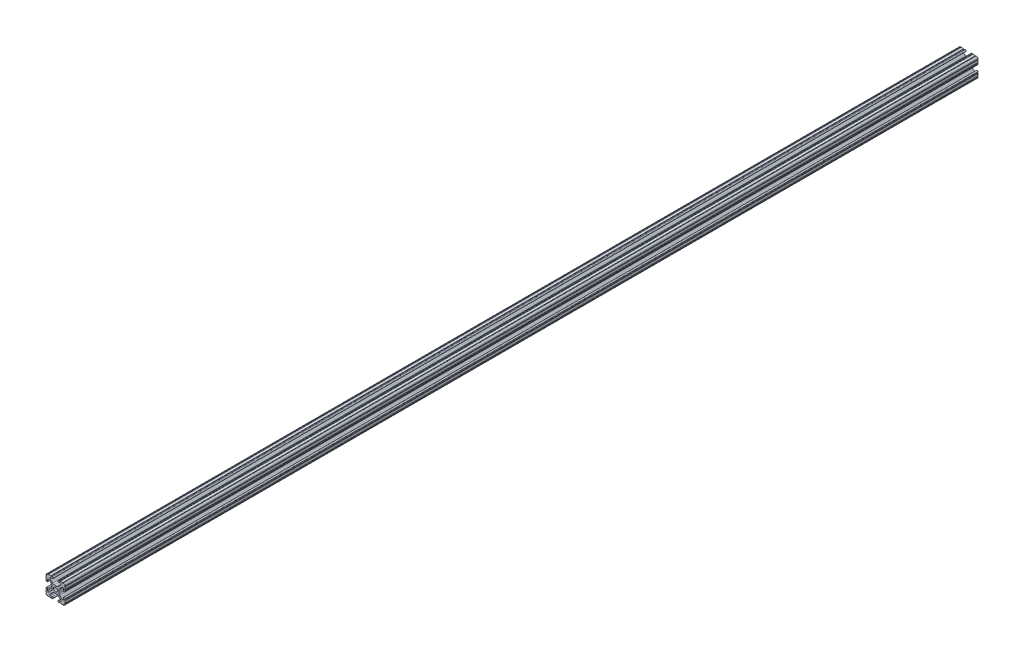
SolidWorks part; units mm, degrees
ref_plane "Front Plane" through (0, 0, 0) normal (0, 0, 1) x (1, 0, 0)
ref_plane "Top Plane" through (0, 0, 0) normal (0, 1, 0) x (1, 0, 0)
ref_plane "Right Plane" through (0, 0, 0) normal (1, 0, 0) x (0, 0, -1)
ref_plane "Plane1" through (0, 0, 0) normal (0, 0, 1) x (1, 0, 0)
sketch "Sketch1" plane through (0, 0, 0) normal (0, 0, 1) x (1, 0, 0)
  line L0 (-12.7, 9.5504) -> (-12.7, 6.3331)
  line L1 (-12.7, 5.3171) -> (-12.7, 4.3434)
  line L2 (-10.4902, 4.3434) -> (-10.4902, 6.4748)
  line L3 (-8.7558, 7.1932) -> (-5.4257, 3.8632)
  line L4 (-4.4958, 1.6181) -> (-4.4958, -1.6181)
  line L5 (-5.4257, -3.8632) -> (-8.7558, -7.1932)
  line L6 (-10.4902, -6.4748) -> (-10.4902, -4.3434)
  line L7 (-12.7, -4.3434) -> (-12.7, -5.3171)
  line L8 (-12.7, -6.3331) -> (-12.7, -9.5504)
  line L9 (-9.5504, -12.7) -> (-6.3331, -12.7)
  line L10 (-5.3171, -12.7) -> (-4.3434, -12.7)
  line L11 (-4.3434, -10.4902) -> (-6.4748, -10.4902)
  line L12 (-7.1932, -8.7558) -> (-3.8632, -5.4257)
  line L13 (-1.6181, -4.4958) -> (1.6181, -4.4958)
  line L14 (3.8632, -5.4257) -> (7.1932, -8.7558)
  line L15 (6.4748, -10.4902) -> (4.3434, -10.4902)
  line L16 (4.3434, -12.7) -> (5.3171, -12.7)
  line L17 (6.3331, -12.7) -> (9.5504, -12.7)
  line L18 (12.7, -9.5504) -> (12.7, -6.3331)
  line L19 (12.7, -5.3171) -> (12.7, -4.3434)
  line L20 (10.4902, -4.3434) -> (10.4902, -6.4748)
  line L21 (8.7558, -7.1932) -> (5.4257, -3.8632)
  line L22 (4.4958, -1.6181) -> (4.4958, 1.6181)
  line L23 (5.4257, 3.8632) -> (8.7558, 7.1932)
  line L24 (10.4902, 6.4748) -> (10.4902, 4.3434)
  line L25 (12.7, 4.3434) -> (12.7, 5.3171)
  line L26 (12.7, 6.3331) -> (12.7, 9.5504)
  line L27 (9.5504, 12.7) -> (6.3331, 12.7)
  line L28 (5.3171, 12.7) -> (4.3434, 12.7)
  line L29 (4.3434, 10.4902) -> (6.4748, 10.4902)
  line L30 (7.1932, 8.7558) -> (3.8632, 5.4257)
  line L31 (1.6181, 4.4958) -> (-1.6181, 4.4958)
  line L32 (-3.8632, 5.4257) -> (-7.1932, 8.7558)
  line L33 (-6.4748, 10.4902) -> (-4.3434, 10.4902)
  line L34 (-4.3434, 12.7) -> (-5.3171, 12.7)
  line L35 (-6.3331, 12.7) -> (-9.5504, 12.7)
  arc A0 (-12.7, 6.3331) -> (-12.7, 5.3171) centre (-12.7, 5.8251) cw
  arc A1 (-12.7, 4.3434) -> (-10.4902, 4.3434) centre (-11.5951, 4.3434) ccw
  arc A2 (-10.4902, 6.4748) -> (-8.7558, 7.1932) centre (-9.4742, 6.4748) cw
  arc A3 (-5.4257, 3.8632) -> (-4.4958, 1.6181) centre (-7.6708, 1.6181) cw
  arc A4 (-4.4958, -1.6181) -> (-5.4257, -3.8632) centre (-7.6708, -1.6181) cw
  arc A5 (-8.7558, -7.1932) -> (-10.4902, -6.4748) centre (-9.4742, -6.4748) cw
  arc A6 (-10.4902, -4.3434) -> (-12.7, -4.3434) centre (-11.5951, -4.3434) ccw
  arc A7 (-12.7, -5.3171) -> (-12.7, -6.3331) centre (-12.7, -5.8251) cw
  arc A8 (-12.7, -9.5504) -> (-12.6998, -10.5664) centre (-12.7, -10.0584) cw
  arc A9 (-12.6998, -10.5664) -> (-10.5664, -12.6998) centre (-10.5918, -10.5918) ccw
  arc A10 (-10.5664, -12.6998) -> (-9.5504, -12.7) centre (-10.0584, -12.7) cw
  arc A11 (-6.3331, -12.7) -> (-5.3171, -12.7) centre (-5.8251, -12.7) cw
  arc A12 (-4.3434, -12.7) -> (-4.3434, -10.4902) centre (-4.3434, -11.5951) ccw
  arc A13 (-6.4748, -10.4902) -> (-7.1932, -8.7558) centre (-6.4748, -9.4742) cw
  arc A14 (-3.8632, -5.4257) -> (-1.6181, -4.4958) centre (-1.6181, -7.6708) cw
  arc A15 (1.6181, -4.4958) -> (3.8632, -5.4257) centre (1.6181, -7.6708) cw
  arc A16 (7.1932, -8.7558) -> (6.4748, -10.4902) centre (6.4748, -9.4742) cw
  arc A17 (4.3434, -10.4902) -> (4.3434, -12.7) centre (4.3434, -11.5951) ccw
  arc A18 (5.3171, -12.7) -> (6.3331, -12.7) centre (5.8251, -12.7) cw
  arc A19 (9.5504, -12.7) -> (10.5664, -12.6998) centre (10.0584, -12.7) cw
  arc A20 (10.5664, -12.6998) -> (12.6998, -10.5664) centre (10.5918, -10.5918) ccw
  arc A21 (12.6998, -10.5664) -> (12.7, -9.5504) centre (12.7, -10.0584) cw
  arc A22 (12.7, -6.3331) -> (12.7, -5.3171) centre (12.7, -5.8251) cw
  arc A23 (12.7, -4.3434) -> (10.4902, -4.3434) centre (11.5951, -4.3434) ccw
  arc A24 (10.4902, -6.4748) -> (8.7558, -7.1932) centre (9.4742, -6.4748) cw
  arc A25 (5.4257, -3.8632) -> (4.4958, -1.6181) centre (7.6708, -1.6181) cw
  arc A26 (4.4958, 1.6181) -> (5.4257, 3.8632) centre (7.6708, 1.6181) cw
  arc A27 (8.7558, 7.1932) -> (10.4902, 6.4748) centre (9.4742, 6.4748) cw
  arc A28 (10.4902, 4.3434) -> (12.7, 4.3434) centre (11.5951, 4.3434) ccw
  arc A29 (12.7, 5.3171) -> (12.7, 6.3331) centre (12.7, 5.8251) cw
  arc A30 (12.7, 9.5504) -> (12.6998, 10.5664) centre (12.7, 10.0584) cw
  arc A31 (12.6998, 10.5664) -> (10.5664, 12.6998) centre (10.5918, 10.5918) ccw
  arc A32 (10.5664, 12.6998) -> (9.5504, 12.7) centre (10.0584, 12.7) cw
  arc A33 (6.3331, 12.7) -> (5.3171, 12.7) centre (5.8251, 12.7) cw
  arc A34 (4.3434, 12.7) -> (4.3434, 10.4902) centre (4.3434, 11.5951) ccw
  arc A35 (6.4748, 10.4902) -> (7.1932, 8.7558) centre (6.4748, 9.4742) cw
  arc A36 (3.8632, 5.4257) -> (1.6181, 4.4958) centre (1.6181, 7.6708) cw
  arc A37 (-1.6181, 4.4958) -> (-3.8632, 5.4257) centre (-1.6181, 7.6708) cw
  arc A38 (-7.1932, 8.7558) -> (-6.4748, 10.4902) centre (-6.4748, 9.4742) cw
  arc A39 (-4.3434, 10.4902) -> (-4.3434, 12.7) centre (-4.3434, 11.5951) ccw
  arc A40 (-5.3171, 12.7) -> (-6.3331, 12.7) centre (-5.8251, 12.7) cw
  arc A41 (-9.5504, 12.7) -> (-10.5664, 12.6998) centre (-10.0584, 12.7) cw
  arc A42 (-10.5664, 12.6998) -> (-12.6998, 10.5664) centre (-10.5918, 10.5918) ccw
  arc A43 (-12.6998, 10.5664) -> (-12.7, 9.5504) centre (-12.7, 10.0584) cw
  circle A44 centre (0, 0) radius 2.6035
extrude "Boss-Extrude1" add sketch "Sketch1" against normal blind 1219.2
